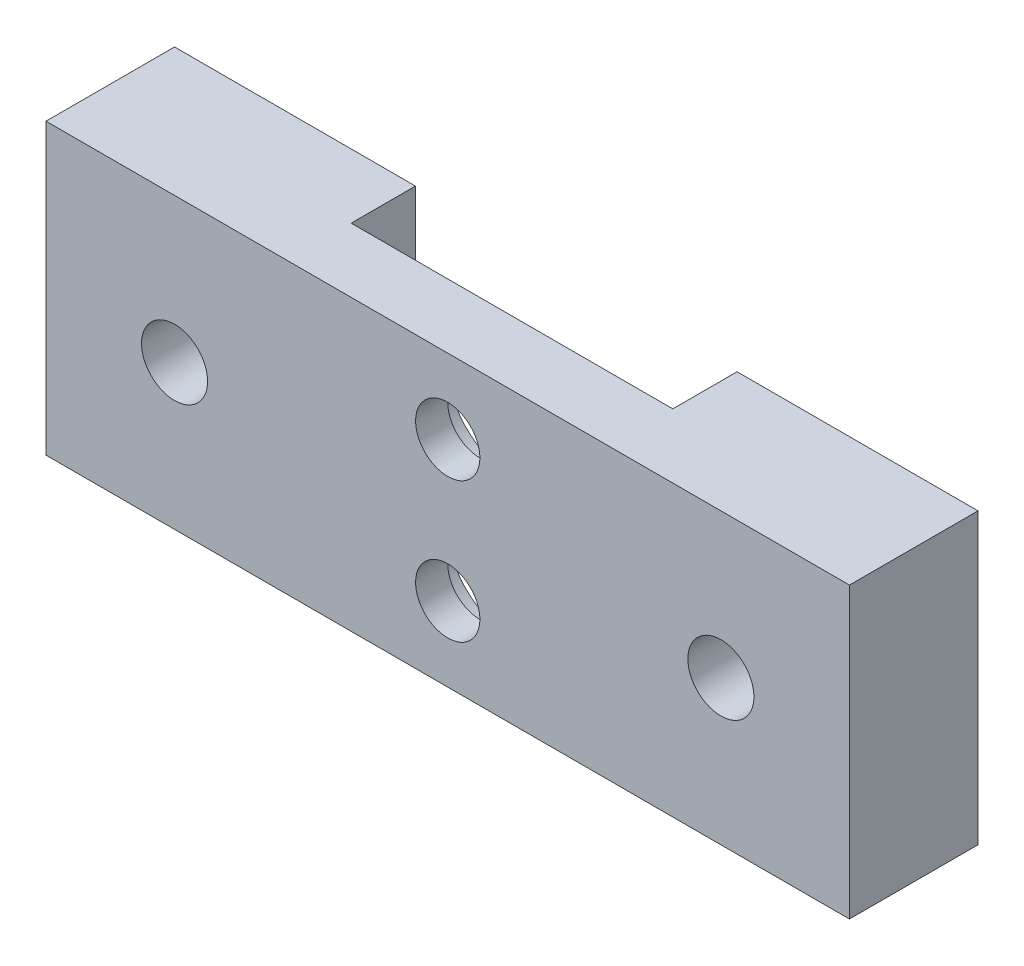
SolidWorks part; units mm, degrees
ref_plane "Front Plane" through (0, 0, 0) normal (0, 0, 1) x (1, 0, 0)
ref_plane "Top Plane" through (0, 0, 0) normal (0, 1, 0) x (1, 0, 0)
ref_plane "Right Plane" through (0, 0, 0) normal (1, 0, 0) x (0, 0, -1)
sketch "Sketch1" plane through (0, 0, 0) normal (0, 1, 0) x (1, 0, 0)
  line L0 (-39.6875, 0) -> (39.6875, 0)
  line L1 (39.6875, 0) -> (39.6875, 12.7)
  line L2 (39.6875, 12.7) -> (15.8877, 12.7)
  line L3 (15.8877, 12.7) -> (15.8877, 6.35)
  line L4 (15.8877, 6.35) -> (-15.8877, 6.35)
  line L5 (-15.8877, 6.35) -> (-15.8877, 12.7)
  line L6 (-15.8877, 12.7) -> (-39.6875, 12.7)
  line L7 (-39.6875, 12.7) -> (-39.6875, 0)
  point P7 (0, 0)
  point P10 (0, 6.35)
  dimension "D1" = 79.375
  dimension "D2" = 12.7
  dimension "D3" = 31.7754
  dimension "D4" = 6.35
extrude "Boss-Extrude1" add sketch "Sketch1" along normal blind 28.575
hole_wizard "Hole1" positions "Sketch2" profile "Sketch3" legacy
sketch "Sketch2" plane through (0, 0, -6.35) normal (0, 0, 1) x (1, 0, 0)
  line L3 (0, 21.1963) -> (0, 7.3787) construction
  point P0 (0, 7.3787)
  point P2 (0, 21.1963)
  point P37 (0, 14.2875)
  dimension "D1" = 13.8176
  dimension "D2" = 21.1963
sketch "Sketch3" plane through (0, 7.3787, -6.35) normal (1, 0, 0) x (0, 1, 0)
  line L0 (0, 0) -> (0, 8.2577) construction
  line L1 (0, 8.2577) -> (3.175, 6.35) construction
  line L2 (3.175, 6.35) -> (3.175, 3.175) construction
  line L3 (3.175, 3.175) -> (6.35, 3.175) construction
  line L4 (6.35, 0) -> (0, 0) construction
  line L5 (0, -11.3109) -> (0, 121.1557) construction
  line L6 (0, 8.2577) -> (-3.175, 6.35) construction
  line L7 (6.35, 3.175) -> (6.35, 0) construction
  line L17 (6.35, 3.175) -> (6.35, 6.35)
  line L18 (6.35, 6.35) -> (0, 6.35)
  line L19 (3.175, 3.175) -> (6.35, 3.175)
  line L20 (3.175, 0) -> (3.175, 3.175)
  line L21 (0, -1.9077) -> (3.175, 0)
  line L22 (0, 6.35) -> (0, -1.9077)
  dimension "Depth" = 6.35
  dimension "Drill Angle" = 118
  dimension "Diameter" = 6.35
  dimension "C-Bore Diameter" = 6.35
  dimension "C-Bore Depth" = 3.175
hole_wizard "5/16-18 Tapped Hole1" positions "Sketch6" profile "Sketch5" tap size "5/16-18" standard "ANSI Inch" end condition through all
sketch "Sketch6" plane through (0, 0, -12.7) normal (0, 0, -1) x (-1, 0, 0)
  line L0 (39.6875, 28.575) -> (39.6875, 0) construction
  line L3 (-39.6875, 28.575) -> (-39.6875, 0) construction
  point P0 (26.9875, 14.2875)
  point P2 (-26.9875, 14.2875)
  point P8 (39.6875, 14.2875)
  point P20 (-39.6875, 14.2875)
  dimension "D1" = 12.7
  dimension "D2" = 12.7
sketch "Sketch5" plane through (-26.9875, 14.2875, -12.7) normal (1, 0, 0) x (0, 1, 0)
  line L0 (0, 0) -> (0, 12.7)
  line L1 (0, 12.7) -> (3.2639, 12.7)
  line L2 (3.2639, 12.7) -> (3.2639, 0)
  line L5 (3.2639, 0) -> (0, 0)
  line L11 (0, -6.35) -> (0, 107.95) construction
  dimension "Thru Tap Drill Dia." = 6.5278
  dimension "Thru Tap Drill Depth" = 12.7
cosmetic thread "Hole Thread1"
cosmetic thread "Hole Thread2"
hole_wizard "Hole4" positions "Sketch15" profile "Sketch16" legacy
sketch "Sketch15" plane through (0, 0, -6.35) normal (0, 0, -1) x (-1, 0, 0)
  line L1 (-15.8877, 0) -> (15.8877, 0) construction
  line L2 (-15.8877, 28.575) -> (15.8877, 28.575) construction
  point P0 (0, 21.1963)
  point P2 (0, 7.3787)
  point P14 (0, 28.575)
  dimension "D1" = 13.8176
  dimension "D2" = 21.1963
sketch "Sketch16" plane through (0, 21.1963, -6.35) normal (1, 0, 0) x (0, 1, 0)
  line L0 (0, 0) -> (0, 8.2577)
  line L1 (0, 8.2577) -> (3.175, 6.35)
  line L2 (3.175, 6.35) -> (3.175, 3.175)
  line L3 (3.175, 3.175) -> (6.35, 3.175)
  line L4 (6.35, 0) -> (0, 0)
  line L5 (0, -11.3109) -> (0, 121.1557) construction
  line L6 (0, 8.2577) -> (-3.175, 6.35) construction
  line L7 (6.35, 3.175) -> (6.35, 0)
  dimension "Depth" = 6.35
  dimension "Drill Angle" = 118
  dimension "Diameter" = 6.35
  dimension "C-Bore Diameter" = 12.7
  dimension "C-Bore Depth" = 3.175
